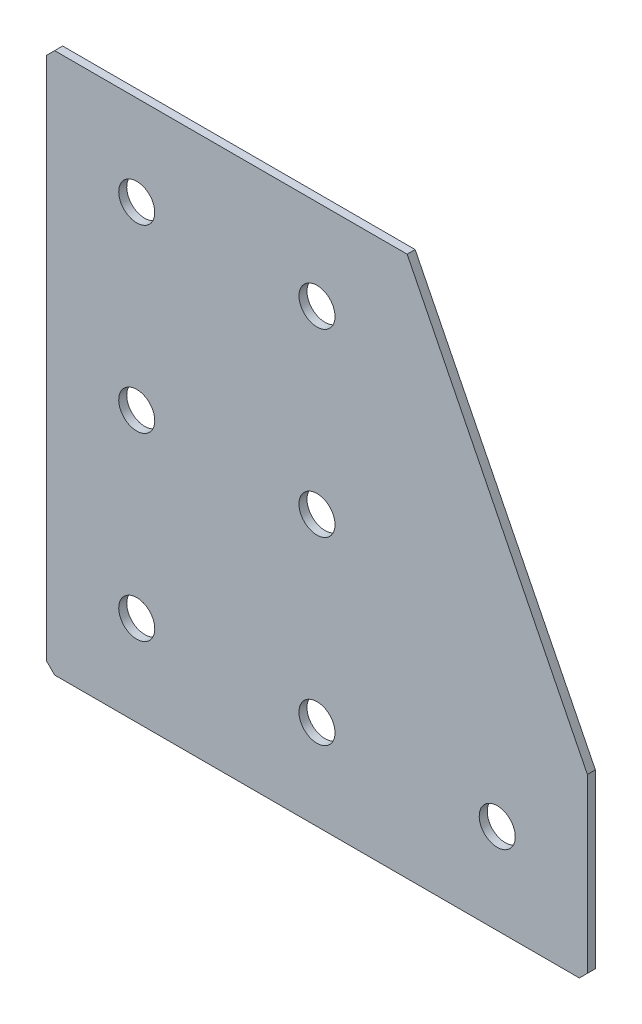
SolidWorks part; units mm, degrees
material "Простая углеродистая сталь"
ref_plane "Спереди(Плоскость XY)" through (0, 0, 0) normal (0, 0, 1) x (1, 0, 0)
ref_plane "Сверху(Плоскость XZ)" through (0, 0, 0) normal (0, 1, 0) x (1, 0, 0)
ref_plane "Справа(Плоскость ZY)" through (0, 0, 0) normal (1, 0, 0) x (0, 0, -1)
sketch "Эскиз1" plane through (0, 0, 0) normal (0, 0, -1) x (1, 0, 0)
  line L0 (0, 0) -> (0, 135)
  line L1 (0, 135) -> (135, 135)
  line L2 (135, 135) -> (135, 90)
  line L3 (135, 90) -> (90, 90) construction
  line L4 (90, 90) -> (90, 0) construction
  line L5 (90, 0) -> (0, 0)
  line L6 (135, 90) -> (90, 0)
  dimension "D1" = 135
  dimension "D2" = 45
  dimension "D3" = 90
extrude "Бобышка-Вытянуть1" add sketch "Эскиз1" along normal blind 2
hole_wizard "Отверстие с зазором M81" positions "Эскиз2" profile "Эскиз3" hole size "M8" standard "IS" end condition through all
sketch "Эскиз2" plane through (0, 0, -2) normal (0, 0, -1) x (1, 0, 0)
  line L0 (22.5, 0) -> (22.5, 135) construction
  line L1 (0, 0) -> (90, 0) construction
  line L2 (135, 135) -> (0, 135) construction
  line L3 (135, 112.5) -> (0, 112.5) construction
  line L4 (135, 90) -> (135, 135) construction
  line L5 (0, 135) -> (0, 0) construction
  point P0 (67.5, 112.5)
  point P2 (22.5, 112.5)
  point P4 (22.5, 67.5)
  point P6 (22.5, 22.5)
  point P21 (112.5, 112.5)
  point P24 (67.5, 67.5)
  point P26 (67.5, 22.5)
  dimension "D1" = 45
  dimension "D2" = 45
  dimension "D3" = 45
  dimension "D4" = 22.5
  dimension "D5" = 45
  dimension "D6" = 22.5
sketch "Эскиз3" plane through (67.5, -112.5, -2) normal (1, 0, 0) x (0, 1, 0)
  line L0 (0, 0) -> (0, 2)
  line L1 (0, 2) -> (4.5, 2)
  line L2 (4.5, 2) -> (4.5, 0)
  line L5 (4.5, 0) -> (0, 0)
  line L11 (0, -6.35) -> (0, 107.95) construction
  dimension "Диаметр сквозного отверстия" = 9
  dimension "Глубина сквозного отверстия" = 2
chamfer "Фаска1" distance 2 angle 45 3 edges at (0, 0, -1) (135, -135, -1) (0, -135, -1)
